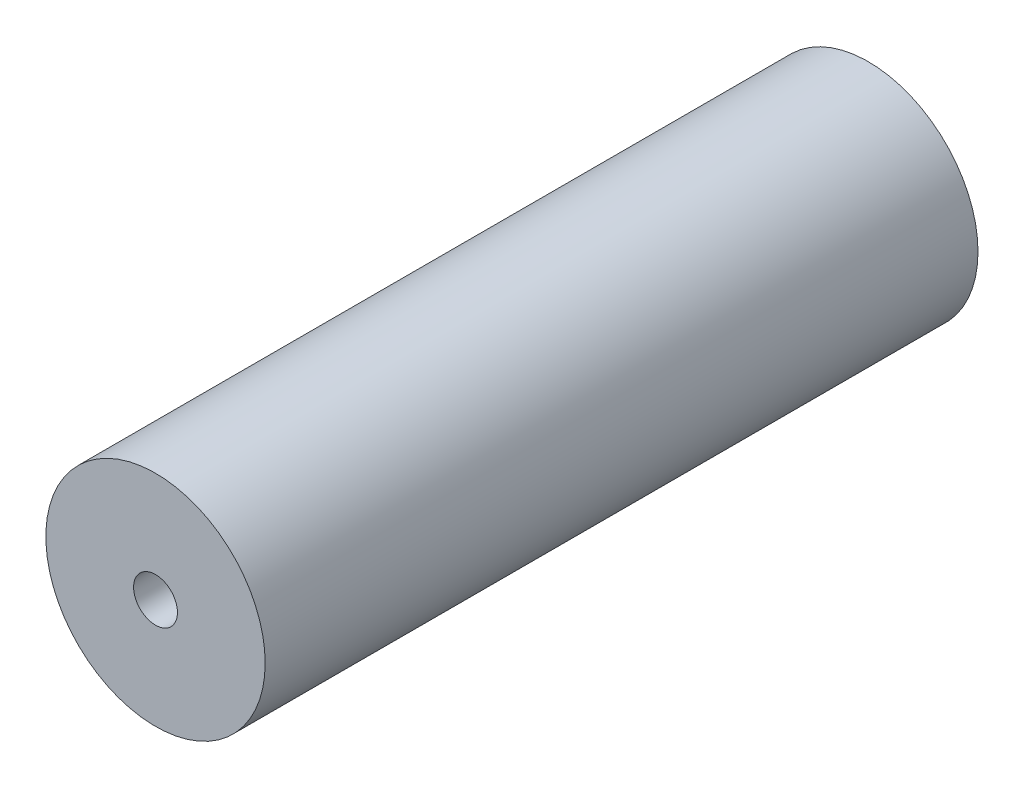
SolidWorks part; units mm, degrees
ref_plane "Front Plane" through (0, 0, 0) normal (0, 0, 1) x (1, 0, 0)
ref_plane "Top Plane" through (0, 0, 0) normal (0, 1, 0) x (1, 0, 0)
ref_plane "Right Plane" through (0, 0, 0) normal (1, 0, 0) x (0, 0, -1)
sketch "Sketch1" plane through (0, 0, 0) normal (0, 0, 1) x (1, 0, 0)
  circle A0 centre (0, 0) radius 2
  circle A1 centre (0, 0) radius 10
  dimension "D1" = 20
  dimension "D2" = 4
extrude "Boss-Extrude1" add sketch "Sketch1" along normal blind 65
